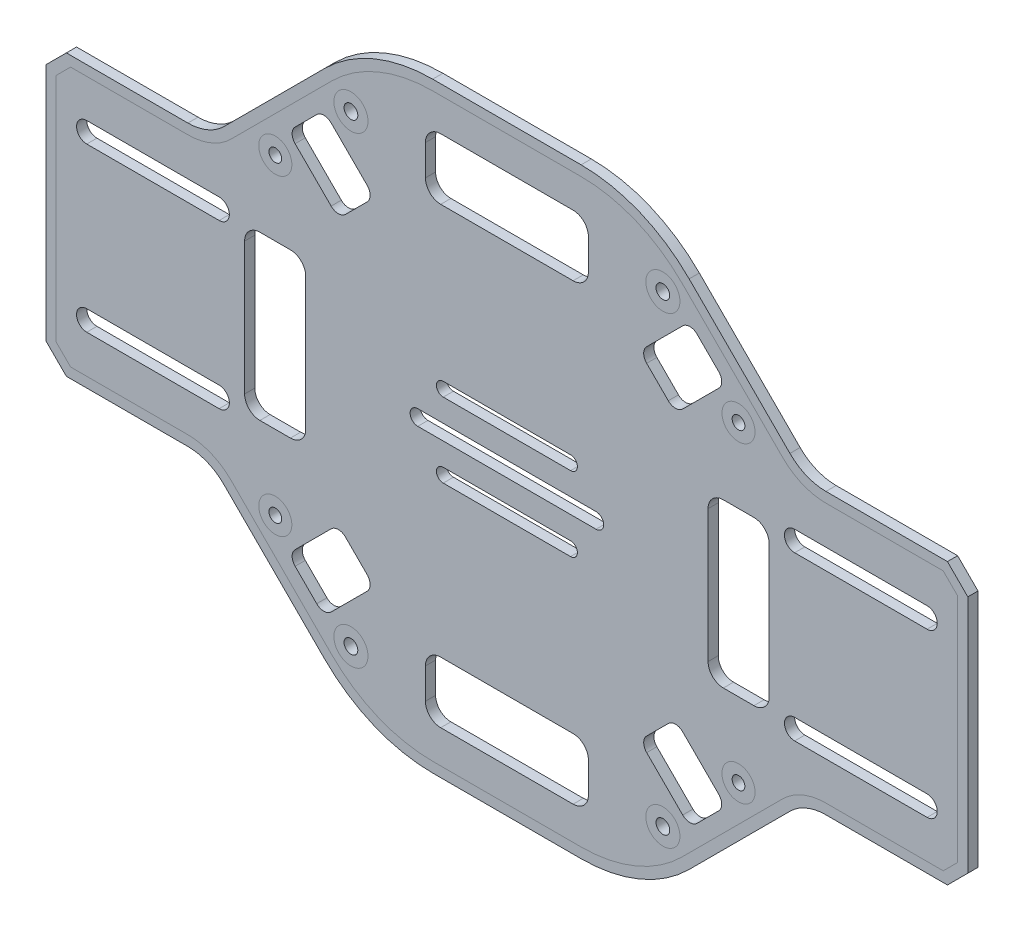
SolidWorks part; units mm, degrees
ref_plane "Ön Düzlem" through (0, 0, 0) normal (0, 0, 1) x (1, 0, 0)
ref_plane "Üst Düzlem" through (0, 0, 0) normal (0, 1, 0) x (1, 0, 0)
ref_plane "Sağ Düzlem" through (0, 0, 0) normal (1, 0, 0) x (0, 0, -1)
sketch "Çizim1" plane through (0, 0, 0) normal (0, 0, 1) x (1, 0, 0)
  line L1 (-12.5, -7.3106) -> (12.5, -7.3106) construction
  line L2 (90.5, -23.5) -> (90.5, 23.5)
  line L3 (-90.5, -23.5) -> (-90.5, 23.5)
  line L4 (-35.7868, 50.2132) -> (-55.5711, 30.4289)
  line L5 (86.5, 27.5) -> (90.5, 23.5)
  line L6 (86.5, 27.5) -> (62.6421, 27.5)
  line L7 (-14.5736, 59) -> (14.5736, 59)
  line L8 (35.7868, 50.2132) -> (55.5711, 30.4289)
  line L9 (-86.5, 27.5) -> (-62.6421, 27.5)
  line L10 (-86.5, 27.5) -> (-90.5, 23.5)
  line L11 (-14.5736, -59) -> (14.5736, -59)
  line L12 (-86.5, -27.5) -> (-90.5, -23.5)
  line L13 (-86.5, -27.5) -> (-62.6421, -27.5)
  line L14 (35.7868, -50.2132) -> (55.5711, -30.4289)
  line L15 (86.5, -27.5) -> (62.6421, -27.5)
  line L16 (86.5, -27.5) -> (90.5, -23.5)
  line L17 (-35.7868, -50.2132) -> (-55.5711, -30.4289)
  line L18 (-82.5, -16) -> (-56.5, -16) construction
  line L19 (-82.5, -14) -> (-56.5, -14)
  line L20 (-82.5, -18) -> (-56.5, -18)
  line L21 (-12.5, -5.9682) -> (12.5, -5.9682)
  line L22 (-12.5, -8.6531) -> (12.5, -8.6531)
  line L23 (-37.3431, -41.5858) -> (-41.5858, -37.3431)
  line L24 (-41.5858, -34.5147) -> (-34.5147, -27.4437)
  line L25 (-31.6863, -27.4437) -> (-27.4437, -31.6863)
  line L26 (-34.5147, -41.5858) -> (-27.4437, -34.5147)
  line L27 (-12.5, 7.3106) -> (12.5, 7.3106) construction
  line L28 (-12.5, 5.9682) -> (12.5, 5.9682)
  line L29 (0, -50.5) -> (13, -50.5)
  line L30 (16, -47.5) -> (16, -41.5)
  line L31 (13, -38.5) -> (-13, -38.5)
  line L32 (-16, -41.5) -> (-16, -47.5)
  line L33 (-13, -50.5) -> (0, -50.5)
  line L34 (-17.5, 0) -> (17.5, 0) construction
  line L35 (-17.5, 1.5) -> (17.5, 1.5)
  line L36 (-17.5, -1.5) -> (17.5, -1.5)
  line L37 (-12.5, 8.6531) -> (12.5, 8.6531)
  line L38 (-82.5, 16) -> (-56.5, 16) construction
  line L39 (-82.5, 14) -> (-56.5, 14)
  line L40 (-82.5, 18) -> (-56.5, 18)
  line L41 (16, 47.5) -> (16, 41.5)
  line L42 (0, 50.5) -> (13, 50.5)
  line L43 (-13, 50.5) -> (0, 50.5)
  line L44 (-16, 41.5) -> (-16, 47.5)
  line L45 (13, 38.5) -> (-13, 38.5)
  line L46 (-34.5147, 41.5858) -> (-27.4437, 34.5147)
  line L47 (-31.6863, 27.4437) -> (-27.4437, 31.6863)
  line L48 (-41.5858, 34.5147) -> (-34.5147, 27.4437)
  line L49 (-37.3431, 41.5858) -> (-41.5858, 37.3431)
  line L50 (82.5, -16) -> (56.5, -16) construction
  line L51 (82.5, -14) -> (56.5, -14)
  line L52 (82.5, -18) -> (56.5, -18)
  line L53 (82.5, 16) -> (56.5, 16) construction
  line L54 (82.5, 14) -> (56.5, 14)
  line L55 (82.5, 18) -> (56.5, 18)
  line L56 (34.5147, -41.5858) -> (27.4437, -34.5147)
  line L57 (31.6863, -27.4437) -> (27.4437, -31.6863)
  line L58 (41.5858, -34.5147) -> (34.5147, -27.4437)
  line L59 (37.3431, -41.5858) -> (41.5858, -37.3431)
  line L60 (37.3431, 41.5858) -> (41.5858, 37.3431)
  line L61 (41.5858, 34.5147) -> (34.5147, 27.4437)
  line L62 (31.6863, 27.4437) -> (27.4437, 31.6863)
  line L63 (34.5147, 41.5858) -> (27.4437, 34.5147)
  line L64 (-51.5, 0) -> (-51.5, -13)
  line L65 (-48.5, -16) -> (-42.5, -16)
  line L66 (-39.5, -13) -> (-39.5, 13)
  line L67 (-42.5, 16) -> (-48.5, 16)
  line L68 (-51.5, 13) -> (-51.5, 0)
  line L69 (51.5, 13) -> (51.5, 0)
  line L70 (42.5, 16) -> (48.5, 16)
  line L71 (39.5, -13) -> (39.5, 13)
  line L72 (48.5, -16) -> (42.5, -16)
  line L73 (51.5, 0) -> (51.5, -13)
  arc A0 (62.6421, 27.5) -> (55.5711, 30.4289) centre (62.6421, 37.5) cw
  arc A1 (14.5736, 59) -> (35.7868, 50.2132) centre (14.5736, 29) cw
  arc A2 (-14.5736, 59) -> (-35.7868, 50.2132) centre (-14.5736, 29) ccw
  arc A3 (-62.6421, 27.5) -> (-55.5711, 30.4289) centre (-62.6421, 37.5) ccw
  arc A4 (-14.5736, -59) -> (-35.7868, -50.2132) centre (-14.5736, -29) cw
  arc A5 (14.5736, -59) -> (35.7868, -50.2132) centre (14.5736, -29) ccw
  arc A6 (-62.6421, -27.5) -> (-55.5711, -30.4289) centre (-62.6421, -37.5) cw
  arc A7 (62.6421, -27.5) -> (55.5711, -30.4289) centre (62.6421, -37.5) ccw
  arc A8 (-82.5, -14) -> (-82.5, -18) centre (-82.5, -16) ccw
  arc A9 (-56.5, -18) -> (-56.5, -14) centre (-56.5, -16) ccw
  arc A10 (-13, -38.5) -> (-16, -41.5) centre (-13, -41.5) ccw
  arc A11 (16, -41.5) -> (13, -38.5) centre (13, -41.5) ccw
  arc A12 (13, -50.5) -> (16, -47.5) centre (13, -47.5) ccw
  arc A13 (-16, -47.5) -> (-13, -50.5) centre (-13, -47.5) ccw
  arc A14 (-41.5858, -37.3431) -> (-41.5858, -34.5147) centre (-40.1716, -35.9289) cw
  arc A15 (-34.5147, -27.4437) -> (-31.6863, -27.4437) centre (-33.1005, -28.8579) cw
  arc A16 (-27.4437, -34.5147) -> (-27.4437, -31.6863) centre (-28.8579, -33.1005) ccw
  arc A17 (-34.5147, -41.5858) -> (-37.3431, -41.5858) centre (-35.9289, -40.1716) cw
  arc A18 (-17.5, 1.5) -> (-17.5, -1.5) centre (-17.5, 0) ccw
  arc A19 (17.5, -1.5) -> (17.5, 1.5) centre (17.5, 0) ccw
  arc A20 (-12.5, -5.9682) -> (-12.5, -8.6531) centre (-12.5, -7.3106) ccw
  arc A21 (12.5, -8.6531) -> (12.5, -5.9682) centre (12.5, -7.3106) ccw
  arc A22 (-12.5, 5.9682) -> (-12.5, 8.6531) centre (-12.5, 7.3106) cw
  arc A23 (12.5, 8.6531) -> (12.5, 5.9682) centre (12.5, 7.3106) cw
  arc A24 (-82.5, 14) -> (-82.5, 18) centre (-82.5, 16) cw
  arc A25 (-56.5, 18) -> (-56.5, 14) centre (-56.5, 16) cw
  arc A26 (13, 50.5) -> (16, 47.5) centre (13, 47.5) cw
  arc A27 (-16, 47.5) -> (-13, 50.5) centre (-13, 47.5) cw
  arc A28 (-34.5147, 41.5858) -> (-37.3431, 41.5858) centre (-35.9289, 40.1716) ccw
  arc A29 (-27.4437, 34.5147) -> (-27.4437, 31.6863) centre (-28.8579, 33.1005) cw
  arc A30 (-34.5147, 27.4437) -> (-31.6863, 27.4437) centre (-33.1005, 28.8579) ccw
  arc A31 (-41.5858, 37.3431) -> (-41.5858, 34.5147) centre (-40.1716, 35.9289) ccw
  arc A32 (16, 41.5) -> (13, 38.5) centre (13, 41.5) cw
  arc A33 (-13, 38.5) -> (-16, 41.5) centre (-13, 41.5) cw
  arc A34 (82.5, -14) -> (82.5, -18) centre (82.5, -16) cw
  arc A35 (56.5, -18) -> (56.5, -14) centre (56.5, -16) cw
  arc A36 (82.5, 14) -> (82.5, 18) centre (82.5, 16) ccw
  arc A37 (56.5, 18) -> (56.5, 14) centre (56.5, 16) ccw
  arc A38 (34.5147, -41.5858) -> (37.3431, -41.5858) centre (35.9289, -40.1716) ccw
  arc A39 (27.4437, -34.5147) -> (27.4437, -31.6863) centre (28.8579, -33.1005) cw
  arc A40 (34.5147, -27.4437) -> (31.6863, -27.4437) centre (33.1005, -28.8579) ccw
  arc A41 (41.5858, -37.3431) -> (41.5858, -34.5147) centre (40.1716, -35.9289) ccw
  arc A42 (41.5858, 37.3431) -> (41.5858, 34.5147) centre (40.1716, 35.9289) cw
  arc A43 (34.5147, 27.4437) -> (31.6863, 27.4437) centre (33.1005, 28.8579) cw
  arc A44 (27.4437, 34.5147) -> (27.4437, 31.6863) centre (28.8579, 33.1005) ccw
  arc A45 (34.5147, 41.5858) -> (37.3431, 41.5858) centre (35.9289, 40.1716) cw
  arc A46 (-39.5, 13) -> (-42.5, 16) centre (-42.5, 13) ccw
  arc A47 (-48.5, 16) -> (-51.5, 13) centre (-48.5, 13) ccw
  arc A48 (-51.5, -13) -> (-48.5, -16) centre (-48.5, -13) ccw
  arc A49 (-42.5, -16) -> (-39.5, -13) centre (-42.5, -13) ccw
  arc A50 (42.5, -16) -> (39.5, -13) centre (42.5, -13) cw
  arc A51 (51.5, -13) -> (48.5, -16) centre (48.5, -13) cw
  arc A52 (48.5, 16) -> (51.5, 13) centre (48.5, 13) cw
  arc A53 (39.5, 13) -> (42.5, 16) centre (42.5, 13) cw
  circle A54 centre (-30.6256, 45.4749) radius 1.35
  circle A55 centre (-45.4749, 30.6256) radius 1.25
  circle A56 centre (45.4749, 30.6256) radius 1.25
  circle A57 centre (30.6256, 45.4749) radius 1.35
  circle A58 centre (-45.4749, -30.6256) radius 1.25
  circle A59 centre (-30.6256, -45.4749) radius 1.35
  circle A60 centre (30.6256, -45.4749) radius 1.35
  circle A61 centre (45.4749, -30.6256) radius 1.25
  point P13 (-69.5, -16)
  point P37 (-90.5, 0)
  point P46 (0, -7.3106)
  point P50 (-29.565, -29.565)
  point P67 (-43, -35.9289)
  point P70 (-33.1005, -26.0294)
  point P73 (-26.0294, -33.1005)
  point P76 (-35.9289, -43)
  point P79 (0, 0)
  point P89 (0, 7.3106)
  point P96 (-69.5, 16)
  point P126 (-26.0294, 33.1005)
  point P127 (-33.1005, 26.0294)
  point P128 (-29.565, 29.565)
  point P131 (69.5, -16)
  point P138 (69.5, 16)
  point P155 (26.0294, -33.1005)
  point P156 (33.1005, -26.0294)
  point P157 (43, -35.9289)
  point P158 (29.565, -29.565)
  point P171 (29.565, 29.565)
  point P172 (33.1005, 26.0294)
  dimension "D1" = 10
  dimension "D2" = 30
  dimension "D3" = 3
  dimension "D4" = 3
  dimension "D5" = 2
extrude "Yükseklik-Ekstrüzyon1" add sketch "Çizim1" along normal blind 2
sketch "Çizim2" plane through (0, 0, 2) normal (0, 0, 1) x (1, 0, 0)
  line L18 (-88.5, 0) -> (-88.5, 22.6716)
  line L19 (-88.5, 22.6716) -> (-85.6716, 25.5)
  line L20 (-85.6716, 25.5) -> (-62.6421, 25.5)
  line L21 (-54.1569, 29.0147) -> (-34.3726, 48.799)
  line L22 (-14.5736, 57) -> (14.5736, 57)
  line L23 (34.3726, 48.799) -> (54.1569, 29.0147)
  line L24 (62.6421, 25.5) -> (85.6716, 25.5)
  line L25 (85.6716, 25.5) -> (88.5, 22.6716)
  line L26 (88.5, 22.6716) -> (88.5, -22.6716)
  line L27 (88.5, -22.6716) -> (85.6716, -25.5)
  line L28 (85.6716, -25.5) -> (62.6421, -25.5)
  line L29 (54.1569, -29.0147) -> (34.3726, -48.799)
  line L30 (14.5736, -57) -> (-14.5736, -57)
  line L31 (-34.3726, -48.799) -> (-54.1569, -29.0147)
  line L32 (-62.6421, -25.5) -> (-85.6716, -25.5)
  line L33 (-85.6716, -25.5) -> (-88.5, -22.6716)
  line L34 (-88.5, -22.6716) -> (-88.5, 0)
  arc A16 (-62.6421, 25.5) -> (-54.1569, 29.0147) centre (-62.6421, 37.5) ccw
  arc A17 (-34.3726, 48.799) -> (-14.5736, 57) centre (-14.5736, 29) cw
  arc A18 (14.5736, 57) -> (34.3726, 48.799) centre (14.5736, 29) cw
  arc A19 (54.1569, 29.0147) -> (62.6421, 25.5) centre (62.6421, 37.5) ccw
  arc A20 (62.6421, -25.5) -> (54.1569, -29.0147) centre (62.6421, -37.5) ccw
  arc A21 (34.3726, -48.799) -> (14.5736, -57) centre (14.5736, -29) cw
  arc A22 (-14.5736, -57) -> (-34.3726, -48.799) centre (-14.5736, -29) cw
  arc A23 (-54.1569, -29.0147) -> (-62.6421, -25.5) centre (-62.6421, -37.5) ccw
  circle A24 centre (45.4749, -30.6256) radius 3.25
  circle A25 centre (30.6256, -45.4749) radius 3.35
  circle A26 centre (-30.6256, -45.4749) radius 3.35
  circle A27 centre (-45.4749, -30.6256) radius 3.25
  circle A28 centre (-45.4749, 30.6256) radius 3.25
  circle A29 centre (-30.6256, 45.4749) radius 3.35
  circle A30 centre (30.6256, 45.4749) radius 3.35
  circle A31 centre (45.4749, 30.6256) radius 3.25
split line "Ayrım Çizgisi1"
sketch "Çizim3" plane through (0, 0, 0) normal (0, 0, -1) x (-1, 0, 0)
  line L41 (88.5, -22.6716) -> (85.0858, -26.0858)
  line L42 (88.5, 22.6716) -> (88.5, -22.6716)
  line L43 (85.6716, 25.5) -> (88.5, 22.6716)
  line L44 (62.6421, 25.5) -> (85.6716, 25.5)
  line L45 (34.3726, 48.799) -> (54.1569, 29.0147)
  line L46 (-14.5736, 57) -> (14.5736, 57)
  line L47 (-54.1569, 29.0147) -> (-34.3726, 48.799)
  line L48 (88.5, -22.6716) -> (85.6716, -25.5)
  line L49 (88.5, 22.6716) -> (88.5, -22.6716)
  line L50 (85.6716, 25.5) -> (88.5, 22.6716)
  line L51 (62.6421, 25.5) -> (85.6716, 25.5)
  line L52 (34.3726, 48.799) -> (54.1569, 29.0147)
  line L53 (-14.5736, 57) -> (14.5736, 57)
  line L54 (-54.1569, 29.0147) -> (-34.3726, 48.799)
  line L60 (14.5736, -57) -> (-14.5736, -57)
  line L61 (54.1569, -29.0147) -> (34.3726, -48.799)
  line L62 (86.5, -25.5) -> (62.6421, -25.5)
  line L63 (14.5736, -57) -> (-14.5736, -57)
  line L64 (54.1569, -29.0147) -> (34.3726, -48.799)
  line L65 (85.6716, -25.5) -> (62.6421, -25.5)
  line L74 (-85.6716, -25.5) -> (-89.0858, -22.0858)
  line L75 (-62.6421, -25.5) -> (-85.6716, -25.5)
  line L76 (-34.3726, -48.799) -> (-54.1569, -29.0147)
  line L77 (-85.6716, -25.5) -> (-88.5, -22.6716)
  line L78 (-62.6421, -25.5) -> (-85.6716, -25.5)
  line L79 (-34.3726, -48.799) -> (-54.1569, -29.0147)
  line L82 (-88.5, 22.6716) -> (-85.0858, 26.0858)
  line L83 (-88.5, -23.5) -> (-88.5, 22.6716)
  line L84 (-88.5, 22.6716) -> (-85.6716, 25.5)
  line L85 (-88.5, -22.6716) -> (-88.5, 22.6716)
  line L91 (-86.5, 25.5) -> (-62.6421, 25.5)
  line L92 (-85.6716, 25.5) -> (-62.6421, 25.5)
  arc A24 (54.1569, 29.0147) -> (62.6421, 25.5) centre (62.6421, 37.5) ccw
  arc A25 (34.3726, 48.799) -> (14.5736, 57) centre (14.5736, 29) ccw
  arc A26 (-14.5736, 57) -> (-34.3726, 48.799) centre (-14.5736, 29) ccw
  arc A27 (54.1569, 29.0147) -> (62.6421, 25.5) centre (62.6421, 37.5) ccw
  arc A28 (34.3726, 48.799) -> (14.5736, 57) centre (14.5736, 29) ccw
  arc A29 (-14.5736, 57) -> (-34.3726, 48.799) centre (-14.5736, 29) ccw
  arc A35 (14.5736, -57) -> (34.3726, -48.799) centre (14.5736, -29) ccw
  arc A36 (62.6421, -25.5) -> (54.1569, -29.0147) centre (62.6421, -37.5) ccw
  arc A37 (14.5736, -57) -> (34.3726, -48.799) centre (14.5736, -29) ccw
  arc A38 (62.6421, -25.5) -> (54.1569, -29.0147) centre (62.6421, -37.5) ccw
  arc A46 (-54.1569, -29.0147) -> (-62.6421, -25.5) centre (-62.6421, -37.5) ccw
  arc A47 (-34.3726, -48.799) -> (-14.5736, -57) centre (-14.5736, -29) ccw
  arc A48 (-54.1569, -29.0147) -> (-62.6421, -25.5) centre (-62.6421, -37.5) ccw
  arc A49 (-34.3726, -48.799) -> (-14.5736, -57) centre (-14.5736, -29) ccw
  arc A53 (-62.6421, 25.5) -> (-54.1569, 29.0147) centre (-62.6421, 37.5) ccw
  arc A54 (-62.6421, 25.5) -> (-54.1569, 29.0147) centre (-62.6421, 37.5) ccw
  circle A92 centre (30.6256, 45.4749) radius 3.35
  circle A93 centre (30.6256, 45.4749) radius 3.35
  circle A95 centre (45.4749, 30.6256) radius 3.25
  circle A96 centre (45.4749, 30.6256) radius 3.25
  circle A101 centre (45.4749, -30.6256) radius 3.25
  circle A102 centre (45.4749, -30.6256) radius 3.25
  circle A104 centre (30.6256, -45.4749) radius 3.35
  circle A105 centre (30.6256, -45.4749) radius 3.35
  circle A107 centre (-30.6256, -45.4749) radius 3.35
  circle A108 centre (-30.6256, -45.4749) radius 3.35
  circle A110 centre (-45.4749, -30.6256) radius 3.25
  circle A111 centre (-45.4749, -30.6256) radius 3.25
  circle A113 centre (-45.4749, 30.6256) radius 3.25
  circle A114 centre (-45.4749, 30.6256) radius 3.25
  circle A116 centre (-30.6256, 45.4749) radius 3.35
  circle A117 centre (-30.6256, 45.4749) radius 3.35
  dimension "D1" = 2
  dimension "D2" = 2
  dimension "D3" = 2
  dimension "D4" = 2
  dimension "D5" = 2
  dimension "D6" = 2
  dimension "D7" = 2
  dimension "D8" = 2
  dimension "D9" = 2
  dimension "D10" = 2
  dimension "D11" = 2
  dimension "D12" = 2
  dimension "D13" = 2
split line "Ayrım Çizgisi2"
